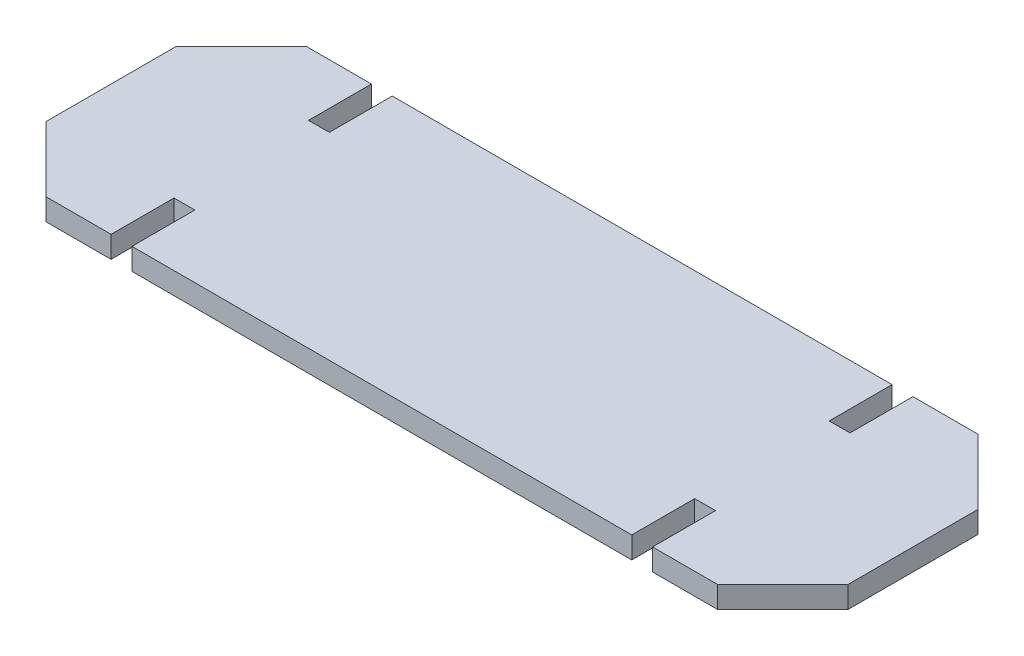
SolidWorks part; units mm, degrees
ref_plane "Front Plane" through (0, 0, 0) normal (0, 0, 1) x (1, 0, 0)
ref_plane "Top Plane" through (0, 0, 0) normal (0, 1, 0) x (1, 0, 0)
ref_plane "Right Plane" through (0, 0, 0) normal (1, 0, 0) x (0, 0, -1)
sketch "Sketch1" plane through (0, 0, 0) normal (0, 1, 0) x (1, 0, 0)
  line L0 (-234.696, 38.1) -> (-196.596, 76.2)
  line L1 (-196.596, 76.2) -> (-158.496, 76.2)
  line L2 (-234.696, 38.1) -> (-234.696, -38.1)
  line L3 (-196.596, -76.2) -> (-158.496, -76.2)
  line L4 (234.696, 38.1) -> (234.696, -38.1)
  line L5 (-234.696, 76.2) -> (234.696, -76.2) construction
  line L6 (-234.696, -76.2) -> (234.696, 76.2) construction
  line L7 (-234.696, -38.1) -> (-196.596, -76.2)
  line L8 (196.596, 76.2) -> (234.696, 38.1)
  line L9 (196.596, -76.2) -> (234.696, -38.1)
  line L10 (146.304, -39.37) -> (158.496, -39.37)
  line L12 (-158.496, -76.2) -> (-158.496, -39.37)
  line L13 (-158.496, -39.37) -> (-146.304, -39.37)
  line L14 (-146.304, -76.2) -> (-146.304, -39.37)
  line L15 (158.496, -76.2) -> (158.496, -39.37)
  line L17 (146.304, -76.2) -> (146.304, -39.37)
  line L18 (-158.496, -39.37) -> (146.304, -39.37) construction
  line L23 (234.696, 0) -> (-234.696, 0) construction
  line L24 (-158.496, 39.37) -> (-146.304, 39.37)
  line L25 (-158.496, 76.2) -> (-158.496, 39.37)
  line L26 (-146.304, 76.2) -> (-146.304, 39.37)
  line L27 (463.296, 76.2) -> (463.296, 39.37)
  line L28 (451.104, 39.37) -> (463.296, 39.37)
  line L29 (451.104, 76.2) -> (451.104, 39.37)
  line L30 (146.304, 76.2) -> (146.304, 39.37)
  line L32 (158.496, 76.2) -> (158.496, 39.37)
  line L33 (146.304, 39.37) -> (158.496, 39.37)
  line L34 (-146.304, 76.2) -> (146.304, 76.2)
  line L35 (-146.304, -76.2) -> (146.304, -76.2)
  line L36 (158.496, -76.2) -> (451.104, -76.2)
  line L37 (158.496, 76.2) -> (451.104, 76.2)
  line L38 (463.296, 76.2) -> (196.596, 76.2)
  line L39 (463.296, -76.2) -> (196.596, -76.2)
  line L40 (-158.496, -76.2) -> (-146.304, -76.2) construction
  line L41 (146.304, -76.2) -> (158.496, -76.2) construction
  line L43 (-196.596, 76.2) -> (-234.696, 76.2) construction
  line L44 (-234.696, 76.2) -> (-234.696, 38.1) construction
  line L45 (-196.596, -76.2) -> (-234.696, -76.2) construction
  line L46 (-234.696, -76.2) -> (-234.696, -38.1) construction
  line L47 (196.596, 76.2) -> (234.696, 76.2) construction
  line L48 (234.696, 76.2) -> (234.696, 38.1) construction
  line L49 (196.596, -76.2) -> (234.696, -76.2) construction
  line L50 (234.696, -76.2) -> (234.696, -38.1) construction
  point P0 (0, 0)
  point P28 (152.4, -39.37)
  point P43 (152.4, 39.37)
extrude "Boss-Extrude1" add sketch "Sketch1" along normal blind 12.7
equation "\"repeat\" = 2"
equation "\"materialThickness\"= .5in"
equation "\"spacing\"= 12in"
equation "\"kirf\"= .01in"
equation "\"D1@Sketch1\"=\"spacing\"/2"
equation "\"D2@Sketch1\"=((\"spacing\"*\"repeat\")-\"spacing\"/2)+(\"materialThickness\"-(\"kirf\"*2))"
equation "\"D4@Sketch1\"=\"materialThickness\"*3"
equation "\"D6@Sketch1\"=\"materialThickness\"*3"
equation "\"D8@Sketch1\"=\"materialThickness\"*3"
equation "\"D10@Sketch1\"=\"materialThickness\"*3"
equation "\"D11@Sketch1\"=\"materialThickness\"*2.9"
equation "\"D12@Sketch1\"=\"materialThickness\"-(\"kirf\"*2)"
equation "\"D13@Sketch1\"=\"spacing\"/4"
equation "\"D14@Sketch1\"=\"repeat\""
equation "\"D15@Sketch1\"=\"spacing\""
equation "\"D1@Boss-Extrude1\"=\"materialThickness\""
